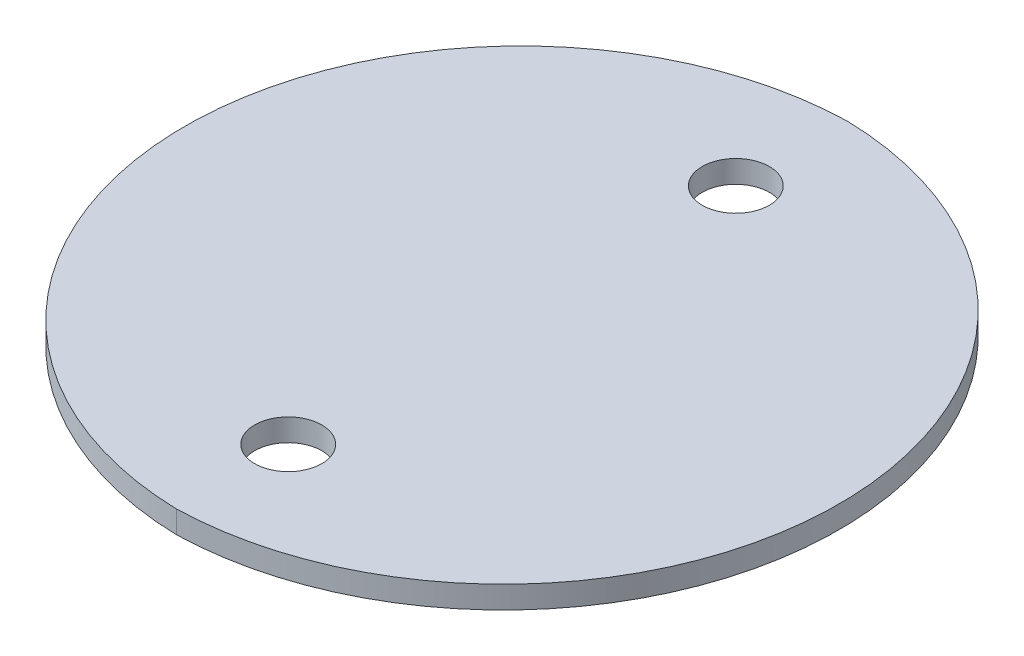
SolidWorks part; units mm, degrees
ref_plane "Front Plane" through (0, 0, 0) normal (0, 0, 1) x (1, 0, 0)
ref_plane "Top Plane" through (0, 0, 0) normal (0, 1, 0) x (1, 0, 0)
ref_plane "Right Plane" through (0, 0, 0) normal (1, 0, 0) x (0, 0, -1)
sketch "Sketch1" plane through (0, 0, 0) normal (0, 1, 0) x (1, 0, 0)
  line L0 (0, -15) -> (0, 15) construction
  line L1 (0, 0) -> (4.5898, 0) construction
  arc A4 (0, 15) -> (0, -15) centre (0.3873, 0) ccw
  arc A5 (0, 15) -> (0, -15) centre (-0.3873, 0) cw
  circle A6 centre (0, 10) radius 1.5
  circle A7 centre (0, -10) radius 1.5
  point P4 (0, 0)
  point P6 (-14.6177, 0)
  point P10 (2.2949, 0)
  dimension "D1" = 30
  dimension "D2" = 15.005
  dimension "D3" = 10
extrude "Boss-Extrude2" add sketch "Sketch1" along normal blind 1
